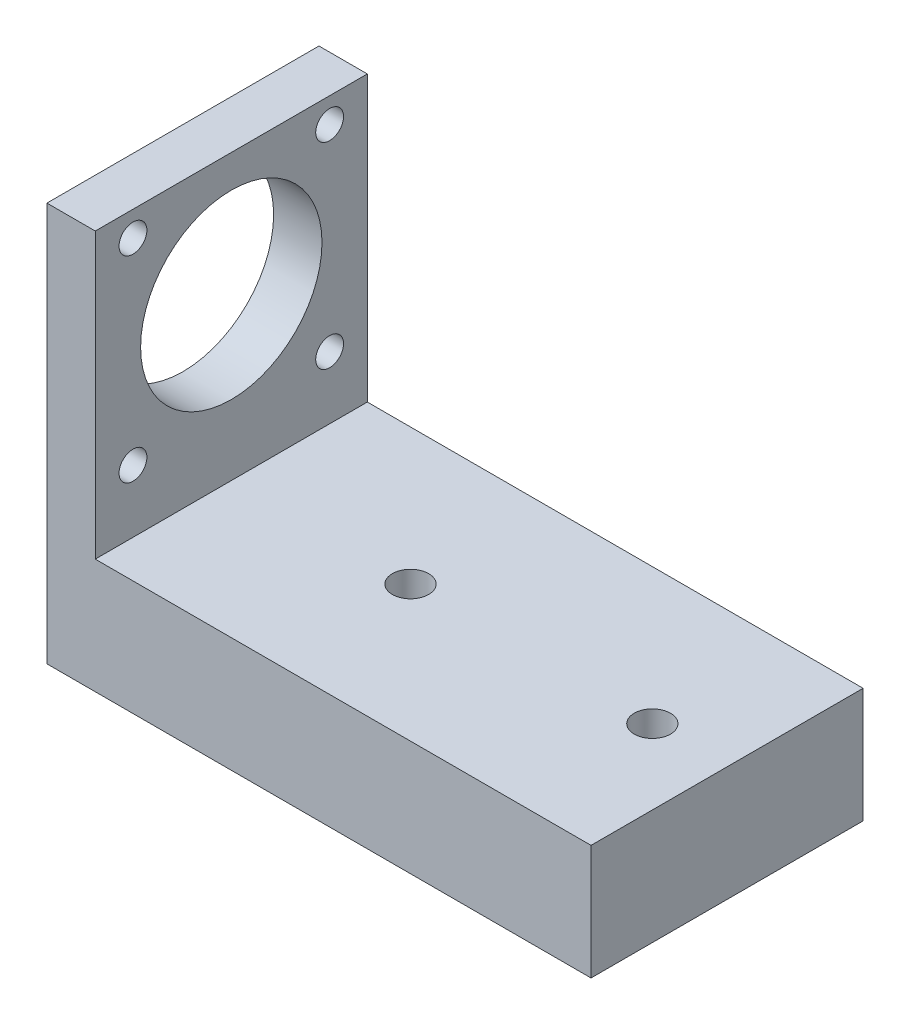
SolidWorks part; units mm, degrees
ref_plane "Front" through (0, 0, 0) normal (0, 0, 1) x (1, 0, 0)
ref_plane "Top" through (0, 0, 0) normal (0, 1, 0) x (1, 0, 0)
ref_plane "Right" through (0, 0, 0) normal (1, 0, 0) x (0, 0, -1)
sketch "Sketch1" plane through (0, 0, 0) normal (0, 1, 0) x (1, 0, 0)
  line L1 (-45, 22.5) -> (45, 22.5)
  line L2 (-45, 22.5) -> (-45, -22.5)
  line L3 (-45, -22.5) -> (45, -22.5)
  line L4 (45, 22.5) -> (45, -22.5)
  line L5 (-45, 22.5) -> (45, -22.5) construction
  line L6 (-45, -22.5) -> (45, 22.5) construction
  point P0 (0, 0)
  dimension "D1" = 45
  dimension "D2" = 90
extrude "Boss-Extrude1" add sketch "Sketch1" along normal blind 5
sketch "Sketch2" plane through (0, 0, 0) normal (0, 1, 0) x (1, 0, 0)
  line L0 (-45, -22.5) -> (45, -22.5) construction
  line L1 (-45, 22.5) -> (-37, 22.5)
  line L2 (-45, 22.5) -> (-45, -22.5)
  line L3 (-45, -22.5) -> (-37, -22.5)
  line L4 (-37, 22.5) -> (-37, -22.5)
  line L6 (45, 22.5) -> (-37, 22.5)
  line L7 (45, 22.5) -> (45, -22.5)
  line L8 (45, -22.5) -> (-37, -22.5)
  line L9 (-37, 22.5) -> (-37, -22.5)
  dimension "D1" = 8
extrude "Boss-Extrude2" add sketch "Sketch2" along normal blind 66 contours L4 L1 L2 L3
sketch "Sketch4" plane through (0, 0, 0) normal (0, 1, 0) x (1, 0, 0)
  line L1 (45, 22.5) -> (-37, 22.5)
  line L2 (45, 22.5) -> (45, -22.5)
  line L3 (45, -22.5) -> (-37, -22.5)
  line L4 (-37, 22.5) -> (-37, -22.5)
extrude "Boss-Extrude3" add sketch "Sketch4" along normal blind 19
sketch "Sketch5" plane through (0, 0, 0) normal (1, 0, 0) x (0, 0, -1)
  line L0 (0, 66) -> (0, -25.5147) construction
  line L1 (22.5, 66) -> (-22.5, 66) construction
  line L2 (0, 50) -> (0, -50) construction
  line L3 (48.4197, 45.6) -> (-58.0691, 45.6) construction
  line L4 (0, 45.6) -> (-39.8425, 85.4425) construction
  circle A0 centre (0, 45.6) radius 15
  circle A2 centre (0, 45.6) radius 23 construction
  circle A3 centre (0, 68.6) radius 2.3 construction
  circle A4 centre (16.2635, 61.8635) radius 2.3
  circle A5 centre (23, 45.6) radius 2.3 [skipped]
  circle A6 centre (16.2635, 29.3365) radius 2.3
  circle A7 centre (0, 22.6) radius 2.3 [skipped]
  circle A8 centre (-16.2635, 29.3365) radius 2.3
  circle A9 centre (-23, 45.6) radius 2.3 [skipped]
  circle A10 centre (-16.2635, 61.8635) radius 2.3
  point P32 (0, 45.6)
  dimension "D3" = 30
  dimension "D4" = 46
  dimension "D7" = 4.6
  dimension "D1" = 20.4
  dimension "D2" = 20.4
  dimension "D5" = 45
  dimension "D6" = 8
extrude "Cut-Extrude1" cut sketch "Sketch5" against normal blind 55
sketch "Sketch6" plane through (0, 0, 0) normal (0, 1, 0) x (1, 0, 0)
  line L0 (-50, 0) -> (50, 0) construction
  circle A0 centre (32.6413, 0) radius 3
  circle A1 centre (-7.3587, 0) radius 3
  dimension "D1" = 6
  dimension "D2" = 6
  dimension "D3" = 40
extrude "Cut-Extrude2" cut sketch "Sketch6" along normal blind 55
